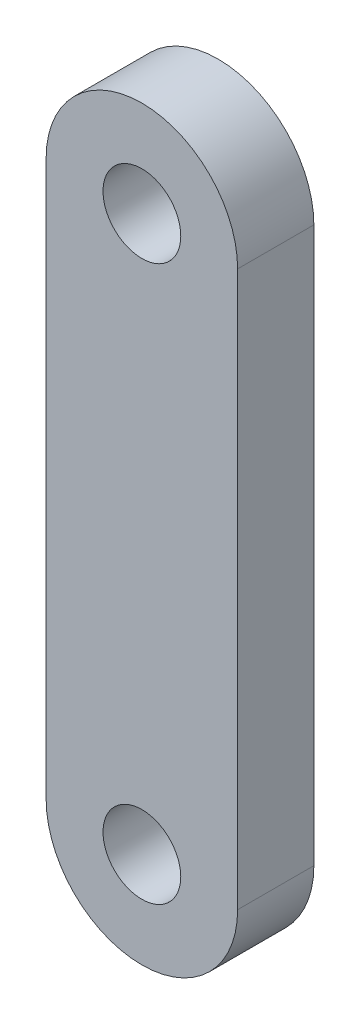
SolidWorks part; units mm, degrees
ref_plane "Front Plane" through (0, 0, 0) normal (0, 0, 1) x (1, 0, 0)
ref_plane "Top Plane" through (0, 0, 0) normal (0, 1, 0) x (1, 0, 0)
ref_plane "Right Plane" through (0, 0, 0) normal (1, 0, 0) x (0, 0, -1)
sketch "Sketch1" plane through (0, 0, 0) normal (0, 0, 1) x (1, 0, 0)
  line L0 (0, 23.114) -> (0, -23.114) construction
  line L1 (7.9756, 23.114) -> (7.9756, -23.114)
  line L2 (-7.9756, 23.114) -> (-7.9756, -23.114)
  arc A0 (7.9756, 23.114) -> (-7.9756, 23.114) centre (0, 23.114) ccw
  arc A1 (-7.9756, -23.114) -> (7.9756, -23.114) centre (0, -23.114) ccw
  circle A2 centre (0, 23.114) radius 3.2385
  circle A3 centre (0, -23.114) radius 3.2385
  point P3 (0, 0)
  dimension "D1" = 6.477
  dimension "D2" = 6.477
  dimension "D3" = 46.228
  dimension "D4" = 15.9512
extrude "Boss-Extrude1" add sketch "Sketch1" along normal blind 6.35
